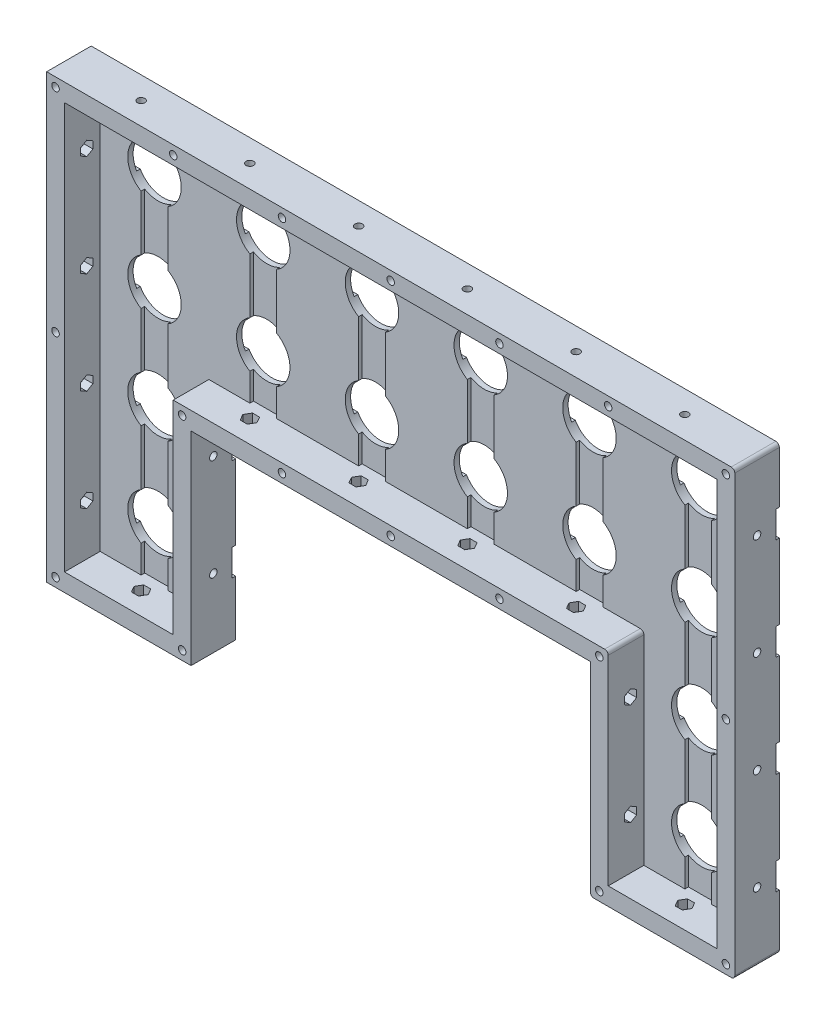
SolidWorks part; units mm, degrees
ref_plane "Alzado" through (0, 0, 0) normal (0, 0, 1) x (1, 0, 0)
ref_plane "Planta" through (0, 0, 0) normal (0, 1, 0) x (1, 0, 0)
ref_plane "Vista lateral" through (0, 0, 0) normal (1, 0, 0) x (0, 0, -1)
sketch "Croquis1" plane through (0, 0, 0) normal (0, 0, 1) x (1, 0, 0)
  line L0 (0, 0) -> (0, 88888.1149) construction
  line L1 (0, 0) -> (88888.1149, 0) construction
  line L2 (-122, -114) -> (-122, 0) construction
  line L3 (-183, 114) -> (183, 114) construction
  line L4 (-183, 114) -> (-183, -114) construction
  line L5 (-183, -114) -> (183, -114) construction
  line L6 (183, 114) -> (183, -114) construction
  line L7 (-183, 114) -> (183, -114) construction
  line L8 (-183, -114) -> (183, 114) construction
  line L9 (-122, 0) -> (0, 0) construction
  line L10 (122, -114) -> (122, 0) construction
  line L11 (-193, -124) -> (193, -124) construction
  line L12 (-193, -124) -> (-193, 124)
  line L13 (-193, 124) -> (193, 124)
  line L14 (193, -124) -> (193, 124)
  line L15 (-193, -124) -> (193, 124) construction
  line L16 (-193, 124) -> (193, -124) construction
  line L17 (-122, 0) -> (122, 0) construction
  line L18 (-122, -114) -> (-183, -114) construction
  line L19 (122, -114) -> (183, -114) construction
  line L20 (-193, -124) -> (-112, -124)
  line L22 (-112, -124) -> (-112, -10)
  line L23 (-112, -10) -> (112, -10)
  line L24 (112, -124) -> (112, -10)
  line L25 (-112, -124) -> (112, -10) construction
  line L26 (-112, -10) -> (112, -124) construction
  line L27 (112, -124) -> (193, -124)
  point P5 (0, 0)
  point P23 (0, -67)
  dimension "D1" = 228
  dimension "D2" = 366
  dimension "D3" = 61
  dimension "D4" = 10
  dimension "D5" = 10
  dimension "D6" = 10
  dimension "D7" = 10
extrude "Saliente-Extruir1" add sketch "Croquis1" along normal blind 25
sketch "Croquis2" plane through (0, 0, 25) normal (0, 0, 1) x (1, 0, 0)
  line L0 (-183, 114) -> (183, 114)
  line L1 (183, 114) -> (183, -114)
  line L2 (183, -114) -> (122, -114)
  line L3 (122, -114) -> (122, 0)
  line L4 (122, 0) -> (-122, 0)
  line L5 (-122, 0) -> (-122, -114)
  line L6 (-122, -114) -> (-183, -114)
  line L7 (-183, -114) -> (-183, 114)
extrude "Cortar-Extruir1" cut sketch "Croquis2" against normal blind 20
sketch "Croquis3" plane through (0, 0, 5) normal (0, 0, 1) x (1, 0, 0)
  line L0 (0, 0) -> (0, 50000) construction
  line L1 (152.5, -114) -> (152.5, 49886) construction
  line L2 (122, -114) -> (183, -114) construction
  line L3 (0, 57) -> (50000, 57) construction
  line L4 (-122, 0) -> (122, 0) construction
  circle A2 centre (30.5, 85.5) radius 15
  circle A3 centre (91.5, 85.5) radius 15
  circle A4 centre (152.5, 85.5) radius 15
  circle A5 centre (91.5, 28.5) radius 15
  circle A6 centre (152.5, 28.5) radius 15
  circle A7 centre (91.5, -28.5) radius 15 [skipped]
  circle A8 centre (152.5, -28.5) radius 15
  circle A9 centre (91.5, -85.5) radius 15 [skipped]
  circle A10 centre (152.5, -85.5) radius 15
  circle A11 centre (30.5, 28.5) radius 15
  circle A12 centre (30.5, -28.5) radius 15 [skipped]
  circle A13 centre (30.5, -85.5) radius 15 [skipped]
  point P7 (152.5, -114)
  dimension "D4" = 30
  dimension "D5" = 3
  dimension "D1" = 61
  dimension "D2" = 57
  dimension "D3" = 57
  dimension "D6" = 4
extrude "Cortar-Extruir2" cut sketch "Croquis3" against normal through all
mirror "Simetría3" about plane through (0, 0, 0) normal (1, 0, 0) of "Cortar-Extruir2"
sketch "Croquis4" plane through (193, 0, 0) normal (1, 0, 0) x (0, 0, -1)
  line L0 (0, -124) -> (0, 124) construction
  line L1 (0, 93) -> (-2, 93)
  line L2 (0, 93) -> (0, 78)
  line L3 (0, 78) -> (-2, 78)
  line L4 (-2, 93) -> (-2, 78)
  line L5 (0, 93) -> (-2, 78) construction
  line L6 (0, 78) -> (-2, 93) construction
  line L7 (0, 0) -> (-50000, 0) construction
  line L8 (0, 36) -> (-2, 36)
  line L9 (0, 36) -> (0, 21)
  line L10 (0, 21) -> (-2, 21)
  line L11 (-2, 36) -> (-2, 21)
  line L12 (0, 36) -> (-2, 21) construction
  line L13 (0, 21) -> (-2, 36) construction
  line L14 (0, -21) -> (-2, -36) construction
  line L19 (0, -36) -> (-2, -21) construction
  line L20 (0, -78) -> (-2, -93) construction
  line L21 (0, -93) -> (-2, -78) construction
  line L22 (-2, -36) -> (-2, -21)
  line L23 (0, -21) -> (-2, -21)
  line L32 (0, -36) -> (0, -21)
  line L33 (0, -36) -> (-2, -36)
  line L34 (-2, -93) -> (-2, -78)
  line L35 (0, -78) -> (-2, -78)
  line L36 (0, -93) -> (0, -78)
  line L37 (0, -93) -> (-2, -93)
  point P4 (-1, 85.5)
  point P11 (-1, 28.5)
  point P24 (-1, -28.5)
  point P25 (-1, -85.5)
  dimension "D1" = 57
  dimension "D2" = 57
  dimension "D3" = 15
  dimension "D4" = 2
extrude "Cortar-Extruir3" cut sketch "Croquis4" against normal through all
sketch "Croquis5" plane through (0, 0, 5) normal (0, 0, 1) x (1, 0, 0)
  line L0 (-152.5, 85.5) -> (-152.5, -49914.5) construction
  line L1 (-91.5, 85.5) -> (-91.5, -49914.5) construction
  line L2 (-30.5, 85.5) -> (-30.5, -49914.5) construction
  line L3 (183, 114) -> (-183, 114) construction
  line L4 (-160, -114) -> (-145, -114)
  line L5 (-160, -114) -> (-160, 114)
  line L6 (-160, 114) -> (-145, 114)
  line L7 (-145, -114) -> (-145, 114)
  line L8 (-160, -114) -> (-145, 114) construction
  line L9 (-160, 114) -> (-145, -114) construction
  line L10 (183, 114) -> (-183, 114) construction
  line L11 (-99, 0) -> (-84, 0)
  line L12 (-99, 0) -> (-99, 114)
  line L13 (-99, 114) -> (-84, 114)
  line L14 (-84, 0) -> (-84, 114)
  line L15 (-99, 0) -> (-84, 114) construction
  line L16 (-99, 114) -> (-84, 0) construction
  line L17 (-122, 0) -> (122, 0) construction
  line L18 (-38, 0) -> (-23, 0)
  line L19 (-38, 0) -> (-38, 114)
  line L20 (-38, 114) -> (-23, 114)
  line L21 (-23, 0) -> (-23, 114)
  line L22 (-38, 0) -> (-23, 114) construction
  line L23 (-38, 114) -> (-23, 0) construction
  line L24 (-183, -114) -> (-122, -114) construction
  point P10 (-152.5, 0)
  point P17 (-91.5, 57)
  point P24 (-30.5, 57)
  dimension "D1" = 15
extrude "Cortar-Extruir4" cut sketch "Croquis5" against normal blind 2
mirror "Simetría4" about plane through (0, 0, 0) normal (1, 0, 0) of "Cortar-Extruir4"
sketch "Croquis6" plane through (0, 124, 0) normal (0, 1, 0) x (1, 0, 0)
  line L0 (0, 0) -> (0, 50000) construction
  line L1 (-203, -12.5) -> (49797, -12.5) construction
  line L2 (-193, -25) -> (-193, 0) construction
  circle A0 centre (30.5, -12.5) radius 2.1
  circle A1 centre (91.5, -12.5) radius 2.1
  circle A2 centre (152.5, -12.5) radius 2.1
  point P9 (-193, -12.5)
  dimension "D1" = 4.2
  dimension "D2" = 61
  dimension "D3" = 61
  dimension "D4" = 61
extrude "Cortar-Extruir5" cut sketch "Croquis6" against normal through all
sketch "Croquis7" plane through (0, 114, 0) normal (0, -1, 0) x (1, 0, 0)
  line L1 (34.4837, 12.5) -> (32.4919, 15.95)
  line L2 (32.4919, 15.95) -> (28.5081, 15.95)
  line L3 (28.5081, 15.95) -> (26.5163, 12.5)
  line L4 (26.5163, 12.5) -> (28.5081, 9.05)
  line L5 (28.5081, 9.05) -> (32.4919, 9.05)
  line L6 (32.4919, 9.05) -> (34.4837, 12.5)
  line L7 (95.4837, 12.5) -> (93.4919, 15.95)
  line L8 (93.4919, 15.95) -> (89.5081, 15.95)
  line L9 (89.5081, 15.95) -> (87.5163, 12.5)
  line L10 (87.5163, 12.5) -> (89.5081, 9.05)
  line L11 (89.5081, 9.05) -> (93.4919, 9.05)
  line L12 (93.4919, 9.05) -> (95.4837, 12.5)
  line L13 (156.4837, 12.5) -> (154.4919, 15.95)
  line L14 (154.4919, 15.95) -> (150.5081, 15.95)
  line L15 (150.5081, 15.95) -> (148.5163, 12.5)
  line L16 (148.5163, 12.5) -> (150.5081, 9.05)
  line L17 (150.5081, 9.05) -> (154.4919, 9.05)
  line L18 (154.4919, 9.05) -> (156.4837, 12.5)
  circle A0 centre (30.5, 12.5) radius 3.45 construction
  circle A1 centre (91.5, 12.5) radius 3.45 construction
  circle A2 centre (152.5, 12.5) radius 3.45 construction
  dimension "D1" = 6.9
extrude "Cortar-Extruir6" cut sketch "Croquis7" against normal offset from surface (5 mm away) 5 up to face at (30.5, 124, 14.6)
sketch "Croquis9" plane through (0, 0, 0) normal (0, 1, 0) x (1, 0, 0)
  line L1 (34.4837, -12.5) -> (32.4919, -9.05)
  line L2 (32.4919, -9.05) -> (28.5081, -9.05)
  line L3 (28.5081, -9.05) -> (26.5163, -12.5)
  line L4 (26.5163, -12.5) -> (28.5081, -15.95)
  line L5 (28.5081, -15.95) -> (32.4919, -15.95)
  line L6 (32.4919, -15.95) -> (34.4837, -12.5)
  line L7 (95.4837, -12.5) -> (93.4919, -9.05)
  line L8 (93.4919, -9.05) -> (89.5081, -9.05)
  line L9 (89.5081, -9.05) -> (87.5163, -12.5)
  line L10 (87.5163, -12.5) -> (89.5081, -15.95)
  line L11 (89.5081, -15.95) -> (93.4919, -15.95)
  line L12 (93.4919, -15.95) -> (95.4837, -12.5)
  circle A0 centre (30.5, -12.5) radius 3.45 construction
  circle A1 centre (91.5, -12.5) radius 3.45 construction
  dimension "D1" = 6.9
extrude "Cortar-Extruir7" cut sketch "Croquis9" against normal offset from surface (5 mm away) 5 up to face at (30.5, -10, 14.6)
sketch "Croquis10" plane through (0, -114, 0) normal (0, 1, 0) x (1, 0, 0)
  line L1 (156.4837, -12.5) -> (154.4919, -9.05)
  line L2 (154.4919, -9.05) -> (150.5081, -9.05)
  line L3 (150.5081, -9.05) -> (148.5163, -12.5)
  line L4 (148.5163, -12.5) -> (150.5081, -15.95)
  line L5 (150.5081, -15.95) -> (154.4919, -15.95)
  line L6 (154.4919, -15.95) -> (156.4837, -12.5)
  circle A0 centre (152.5, -12.5) radius 3.45 construction
  dimension "D1" = 6.9
extrude "Cortar-Extruir8" cut sketch "Croquis10" against normal offset from surface (5 mm away) 5 up to face at (152.5, -124, 14.6)
mirror "Simetría5" about plane through (0, 0, 0) normal (1, 0, 0) of "Cortar-Extruir6", "Cortar-Extruir7", "Cortar-Extruir8", "Cortar-Extruir5"
sketch "Croquis11" plane through (-193, 0, 0) normal (-1, 0, 0) x (0, 0, 1)
  line L0 (12.5, 134) -> (12.5, -49866) construction
  line L1 (25, 124) -> (0, 124) construction
  line L2 (2, 85.5) -> (50002, 85.5) construction
  line L3 (2, 93) -> (2, 78) construction
  circle A0 centre (12.5, 85.5) radius 2.1
  circle A1 centre (12.5, 28.5) radius 2.1
  circle A2 centre (12.5, -28.5) radius 2.1
  circle A3 centre (12.5, -85.5) radius 2.1
  point P4 (12.5, 124)
  point P9 (2, 85.5)
  dimension "D1" = 4.2
  dimension "D2" = 4
extrude "Cortar-Extruir9" cut sketch "Croquis11" against normal through all
sketch "Croquis12" plane through (-183, 0, 0) normal (1, 0, 0) x (0, 0, -1)
  line L1 (-12.5, 81.5163) -> (-9.05, 83.5081)
  line L2 (-9.05, 83.5081) -> (-9.05, 87.4919)
  line L3 (-9.05, 87.4919) -> (-12.5, 89.4837)
  line L4 (-12.5, 89.4837) -> (-15.95, 87.4919)
  line L5 (-15.95, 87.4919) -> (-15.95, 83.5081)
  line L6 (-15.95, 83.5081) -> (-12.5, 81.5163)
  line L7 (-12.5, 24.5163) -> (-9.05, 26.5081)
  line L8 (-9.05, 26.5081) -> (-9.05, 30.4919)
  line L9 (-9.05, 30.4919) -> (-12.5, 32.4837)
  line L10 (-12.5, 32.4837) -> (-15.95, 30.4919)
  line L11 (-15.95, 30.4919) -> (-15.95, 26.5081)
  line L12 (-15.95, 26.5081) -> (-12.5, 24.5163)
  line L13 (-12.5, -32.4837) -> (-9.05, -30.4919)
  line L14 (-9.05, -30.4919) -> (-9.05, -26.5081)
  line L15 (-9.05, -26.5081) -> (-12.5, -24.5163)
  line L16 (-12.5, -24.5163) -> (-15.95, -26.5081)
  line L17 (-15.95, -26.5081) -> (-15.95, -30.4919)
  line L18 (-15.95, -30.4919) -> (-12.5, -32.4837)
  line L19 (-12.5, -89.4837) -> (-9.05, -87.4919)
  line L20 (-9.05, -87.4919) -> (-9.05, -83.5081)
  line L21 (-9.05, -83.5081) -> (-12.5, -81.5163)
  line L22 (-12.5, -81.5163) -> (-15.95, -83.5081)
  line L23 (-15.95, -83.5081) -> (-15.95, -87.4919)
  line L24 (-15.95, -87.4919) -> (-12.5, -89.4837)
  circle A0 centre (-12.5, 85.5) radius 3.45 construction
  circle A1 centre (-12.5, 28.5) radius 3.45 construction
  circle A2 centre (-12.5, -28.5) radius 3.45 construction
  circle A3 centre (-12.5, -85.5) radius 3.45 construction
  dimension "D1" = 6.9
extrude "Cortar-Extruir10" cut sketch "Croquis12" against normal offset from surface (5 mm away) 5 up to face at (-193, 85.5, 14.6)
sketch "Croquis13" plane through (183, 0, 0) normal (-1, 0, 0) x (0, 0, 1)
  line L0 (12.5, 24.5163) -> (15.95, 26.5081)
  line L1 (12.5, 81.5163) -> (15.95, 83.5081)
  line L2 (15.95, 83.5081) -> (15.95, 87.4919)
  line L3 (15.95, 87.4919) -> (12.5, 89.4837)
  line L4 (12.5, 89.4837) -> (9.05, 87.4919)
  line L5 (9.05, 87.4919) -> (9.05, 83.5081)
  line L6 (9.05, 83.5081) -> (12.5, 81.5163)
  line L7 (15.95, 26.5081) -> (15.95, 30.4919)
  line L8 (15.95, 30.4919) -> (12.5, 32.4837)
  line L9 (12.5, 32.4837) -> (9.05, 30.4919)
  line L10 (9.05, 30.4919) -> (9.05, 26.5081)
  line L11 (9.05, 26.5081) -> (12.5, 24.5163)
  line L12 (12.5, -32.4837) -> (15.95, -30.4919)
  line L13 (15.95, -30.4919) -> (15.95, -26.5081)
  line L14 (15.95, -26.5081) -> (12.5, -24.5163)
  line L15 (12.5, -24.5163) -> (9.05, -26.5081)
  line L16 (9.05, -26.5081) -> (9.05, -30.4919)
  line L17 (9.05, -30.4919) -> (12.5, -32.4837)
  line L18 (12.5, -89.4837) -> (15.95, -87.4919)
  line L19 (15.95, -87.4919) -> (15.95, -83.5081)
  line L20 (15.95, -83.5081) -> (12.5, -81.5163)
  line L21 (12.5, -81.5163) -> (9.05, -83.5081)
  line L22 (9.05, -83.5081) -> (9.05, -87.4919)
  line L23 (9.05, -87.4919) -> (12.5, -89.4837)
  circle A0 centre (12.5, 85.5) radius 3.45 construction
  circle A1 centre (12.5, 28.5) radius 3.45 construction
  circle A2 centre (12.5, -28.5) radius 3.45 construction
  circle A3 centre (12.5, -85.5) radius 3.45 construction
  dimension "D1" = 6.9
  dimension "D2" = 4
extrude "Cortar-Extruir11" cut sketch "Croquis13" against normal offset from surface (5 mm away) 5 up to face at (193, 85.5, 14.6)
sketch "Croquis14" plane through (122, 0, 0) normal (1, 0, 0) x (0, 0, -1)
  line L1 (-12.5, -81.5163) -> (-15.95, -83.5081)
  line L2 (-15.95, -83.5081) -> (-15.95, -87.4919)
  line L3 (-15.95, -87.4919) -> (-12.5, -89.4837)
  line L4 (-12.5, -89.4837) -> (-9.05, -87.4919)
  line L5 (-9.05, -87.4919) -> (-9.05, -83.5081)
  line L6 (-9.05, -83.5081) -> (-12.5, -81.5163)
  line L7 (-12.5, -24.5163) -> (-15.95, -26.5081)
  line L8 (-15.95, -26.5081) -> (-15.95, -30.4919)
  line L9 (-15.95, -30.4919) -> (-12.5, -32.4837)
  line L10 (-12.5, -32.4837) -> (-9.05, -30.4919)
  line L11 (-9.05, -30.4919) -> (-9.05, -26.5081)
  line L12 (-9.05, -26.5081) -> (-12.5, -24.5163)
  circle A0 centre (-12.5, -85.5) radius 3.45 construction
  circle A1 centre (-12.5, -28.5) radius 3.45 construction
  dimension "D1" = 6.9
extrude "Cortar-Extruir12" cut sketch "Croquis14" against normal offset from surface (5 mm away) 5 up to face at (112, -28.5, 10.4)
sketch "Croquis15" plane through (-122, 0, 0) normal (-1, 0, 0) x (0, 0, 1)
  line L1 (12.5, -81.5163) -> (9.05, -83.5081)
  line L2 (9.05, -83.5081) -> (9.05, -87.4919)
  line L3 (9.05, -87.4919) -> (12.5, -89.4837)
  line L4 (12.5, -89.4837) -> (15.95, -87.4919)
  line L5 (15.95, -87.4919) -> (15.95, -83.5081)
  line L6 (15.95, -83.5081) -> (12.5, -81.5163)
  line L7 (12.5, -24.5163) -> (9.05, -26.5081)
  line L8 (9.05, -26.5081) -> (9.05, -30.4919)
  line L9 (9.05, -30.4919) -> (12.5, -32.4837)
  line L10 (12.5, -32.4837) -> (15.95, -30.4919)
  line L11 (15.95, -30.4919) -> (15.95, -26.5081)
  line L12 (15.95, -26.5081) -> (12.5, -24.5163)
  circle A0 centre (12.5, -85.5) radius 3.45 construction
  circle A1 centre (12.5, -28.5) radius 3.45 construction
  dimension "D1" = 6.9
extrude "Cortar-Extruir13" cut sketch "Croquis15" against normal offset from surface (5 mm away) 5 up to face at (-112, -28.5, 14.6)
sketch "Croquis16" plane through (0, 0, 25) normal (0, 0, 1) x (1, 0, 0)
  line L0 (-193, 119) -> (49807, 119) construction
  line L1 (0, 0) -> (0, 50000) construction
  line L2 (-188, 124) -> (-188, -49876) construction
  line L3 (-122, 114) -> (-122, 50114) construction
  line L4 (193, 124) -> (-193, 124) construction
  line L5 (-193, 124) -> (-193, -124) construction
  line L6 (-99, 114) -> (-145, 114) construction
  line L7 (-61, 114) -> (-61, 50114) construction
  line L8 (-38, 114) -> (-84, 114) construction
  line L9 (-99, 57) -> (49901, 57) construction
  line L10 (-99, 72.5096) -> (-99, 41.4904) construction
  line L11 (-160, 0) -> (-233.5168, 0) construction
  line L13 (188, 119) -> (188, -49881) construction
  line L14 (-61, -5) -> (49939, -5) construction
  line L15 (117, -124) -> (117, 49876) construction
  line L17 (-117, -124) -> (-117, 49876) construction
  line L19 (-188, -119) -> (49812, -119) construction
  line L20 (112, -10) -> (112, -124) construction
  line L21 (-112, -124) -> (-112, -10) construction
  circle A0 centre (-188, 119) radius 2.1
  circle A1 centre (-122, 119) radius 2.1
  circle A2 centre (-61, 119) radius 2.1
  circle A3 centre (0, 119) radius 2.1
  circle A4 centre (188, 119) radius 2.1
  circle A5 centre (122, 119) radius 2.1
  circle A6 centre (61, 119) radius 2.1
  circle A7 centre (61, -5) radius 2.1
  circle A8 centre (0, -5) radius 2.1
  circle A9 centre (-61, -5) radius 2.1
  circle A10 centre (188, -119) radius 2.1
  circle A11 centre (-188, -119) radius 2.1
  circle A12 centre (-188, 0) radius 2.1
  circle A13 centre (188, 0) radius 2.1
  circle A14 centre (-117, -119) radius 2.1
  circle A15 centre (-117, -5) radius 2.1
  circle A16 centre (117, -5) radius 2.1
  circle A17 centre (117, -119) radius 2.1
  point P17 (-122, 114)
  point P22 (-61, 114)
  point P39 (-99, 57)
  dimension "D3" = 4.2
  dimension "D1" = 5
  dimension "D2" = 5
  dimension "D4" = 5
  dimension "D5" = 5
extrude "Cortar-Extruir14" cut sketch "Croquis16" against normal through all
sketch "Croquis17" plane through (0, 0, 0) normal (0, 0, -1) x (-1, 0, 0)
  line L1 (-184.0163, 119) -> (-186.0081, 122.45)
  line L2 (-186.0081, 122.45) -> (-189.9919, 122.45)
  line L3 (-189.9919, 122.45) -> (-191.9837, 119)
  line L4 (-191.9837, 119) -> (-189.9919, 115.55)
  line L5 (-189.9919, 115.55) -> (-186.0081, 115.55)
  line L6 (-186.0081, 115.55) -> (-184.0163, 119)
  line L7 (-118.0163, 119) -> (-120.0081, 122.45)
  line L8 (-120.0081, 122.45) -> (-123.9919, 122.45)
  line L9 (-123.9919, 122.45) -> (-125.9837, 119)
  line L10 (-125.9837, 119) -> (-123.9919, 115.55)
  line L11 (-123.9919, 115.55) -> (-120.0081, 115.55)
  line L12 (-120.0081, 115.55) -> (-118.0163, 119)
  line L13 (-57.0163, 119) -> (-59.0081, 122.45)
  line L14 (-59.0081, 122.45) -> (-62.9919, 122.45)
  line L15 (-62.9919, 122.45) -> (-64.9837, 119)
  line L16 (-64.9837, 119) -> (-62.9919, 115.55)
  line L17 (-62.9919, 115.55) -> (-59.0081, 115.55)
  line L18 (-59.0081, 115.55) -> (-57.0163, 119)
  line L19 (4.4368, 119) -> (2.2184, 122.8423)
  line L20 (2.2184, 122.8423) -> (-2.2184, 122.8423)
  line L21 (-2.2184, 122.8423) -> (-4.4368, 119)
  line L22 (-4.4368, 119) -> (-2.2184, 115.1577)
  line L23 (-2.2184, 115.1577) -> (2.2184, 115.1577)
  line L24 (2.2184, 115.1577) -> (4.4368, 119)
  line L25 (65.91, 119) -> (63.455, 123.2521)
  line L26 (63.455, 123.2521) -> (58.545, 123.2521)
  line L27 (58.545, 123.2521) -> (56.09, 119)
  line L28 (56.09, 119) -> (58.545, 114.7479)
  line L29 (58.545, 114.7479) -> (63.455, 114.7479)
  line L30 (63.455, 114.7479) -> (65.91, 119)
  line L31 (126.8191, 119) -> (124.4096, 123.1735)
  line L32 (124.4096, 123.1735) -> (119.5904, 123.1735)
  line L33 (119.5904, 123.1735) -> (117.1809, 119)
  line L34 (117.1809, 119) -> (119.5904, 114.8265)
  line L35 (119.5904, 114.8265) -> (124.4096, 114.8265)
  line L36 (124.4096, 114.8265) -> (126.8191, 119)
  line L37 (191.7739, 119) -> (189.8835, 122.2743)
  line L38 (189.8835, 122.2743) -> (186.1026, 122.2743)
  line L39 (186.1026, 122.2743) -> (184.2122, 119)
  line L40 (184.2122, 119) -> (186.1026, 115.7257)
  line L41 (186.1026, 115.7257) -> (189.8835, 115.7257)
  line L42 (189.8835, 115.7257) -> (191.7739, 119)
  line L43 (191.9837, 0) -> (189.9919, 3.45)
  line L44 (189.9919, 3.45) -> (186.0081, 3.45)
  line L45 (186.0081, 3.45) -> (184.0163, 0)
  line L46 (184.0163, 0) -> (186.0081, -3.45)
  line L47 (186.0081, -3.45) -> (189.9919, -3.45)
  line L48 (189.9919, -3.45) -> (191.9837, 0)
  line L49 (191.9837, -119) -> (189.9919, -115.55)
  line L50 (189.9919, -115.55) -> (186.0081, -115.55)
  line L51 (186.0081, -115.55) -> (184.0163, -119)
  line L52 (184.0163, -119) -> (186.0081, -122.45)
  line L53 (186.0081, -122.45) -> (189.9919, -122.45)
  line L54 (189.9919, -122.45) -> (191.9837, -119)
  line L55 (120.9837, -119) -> (118.9919, -115.55)
  line L56 (118.9919, -115.55) -> (115.0081, -115.55)
  line L57 (115.0081, -115.55) -> (113.0163, -119)
  line L58 (113.0163, -119) -> (115.0081, -122.45)
  line L59 (115.0081, -122.45) -> (118.9919, -122.45)
  line L60 (118.9919, -122.45) -> (120.9837, -119)
  line L61 (120.9837, -5) -> (118.9919, -1.55)
  line L62 (118.9919, -1.55) -> (115.0081, -1.55)
  line L63 (115.0081, -1.55) -> (113.0163, -5)
  line L64 (113.0163, -5) -> (115.0081, -8.45)
  line L65 (115.0081, -8.45) -> (118.9919, -8.45)
  line L66 (118.9919, -8.45) -> (120.9837, -5)
  line L67 (64.9837, -5) -> (62.9919, -1.55)
  line L68 (62.9919, -1.55) -> (59.0081, -1.55)
  line L69 (59.0081, -1.55) -> (57.0163, -5)
  line L70 (57.0163, -5) -> (59.0081, -8.45)
  line L71 (59.0081, -8.45) -> (62.9919, -8.45)
  line L72 (62.9919, -8.45) -> (64.9837, -5)
  line L73 (-57.0163, -5) -> (-59.0081, -1.55)
  line L74 (-59.0081, -1.55) -> (-62.9919, -1.55)
  line L75 (-62.9919, -1.55) -> (-64.9837, -5)
  line L76 (-64.9837, -5) -> (-62.9919, -8.45)
  line L77 (-62.9919, -8.45) -> (-59.0081, -8.45)
  line L78 (-59.0081, -8.45) -> (-57.0163, -5)
  line L79 (3.9837, -5) -> (1.9919, -1.55)
  line L80 (1.9919, -1.55) -> (-1.9919, -1.55)
  line L81 (-1.9919, -1.55) -> (-3.9837, -5)
  line L82 (-3.9837, -5) -> (-1.9919, -8.45)
  line L83 (-1.9919, -8.45) -> (1.9919, -8.45)
  line L84 (1.9919, -8.45) -> (3.9837, -5)
  line L85 (-113.0163, -5) -> (-115.0081, -1.55)
  line L86 (-115.0081, -1.55) -> (-118.9919, -1.55)
  line L87 (-118.9919, -1.55) -> (-120.9837, -5)
  line L88 (-120.9837, -5) -> (-118.9919, -8.45)
  line L89 (-118.9919, -8.45) -> (-115.0081, -8.45)
  line L90 (-115.0081, -8.45) -> (-113.0163, -5)
  line L91 (-184.0163, 0) -> (-186.0081, 3.45)
  line L92 (-186.0081, 3.45) -> (-189.9919, 3.45)
  line L93 (-189.9919, 3.45) -> (-191.9837, 0)
  line L94 (-191.9837, 0) -> (-189.9919, -3.45)
  line L95 (-189.9919, -3.45) -> (-186.0081, -3.45)
  line L96 (-186.0081, -3.45) -> (-184.0163, 0)
  line L97 (-184.0163, -119) -> (-186.0081, -115.55)
  line L98 (-186.0081, -115.55) -> (-189.9919, -115.55)
  line L99 (-189.9919, -115.55) -> (-191.9837, -119)
  line L100 (-191.9837, -119) -> (-189.9919, -122.45)
  line L101 (-189.9919, -122.45) -> (-186.0081, -122.45)
  line L102 (-186.0081, -122.45) -> (-184.0163, -119)
  line L103 (-113.0163, -119) -> (-115.0081, -115.55)
  line L104 (-115.0081, -115.55) -> (-118.9919, -115.55)
  line L105 (-118.9919, -115.55) -> (-120.9837, -119)
  line L106 (-120.9837, -119) -> (-118.9919, -122.45)
  line L107 (-118.9919, -122.45) -> (-115.0081, -122.45)
  line L108 (-115.0081, -122.45) -> (-113.0163, -119)
  circle A0 centre (-188, 119) radius 3.45 construction
  circle A1 centre (-122, 119) radius 3.45 construction
  circle A2 centre (-61, 119) radius 3.45 construction
  circle A3 centre (0, 119) radius 3.8423 construction
  circle A4 centre (61, 119) radius 4.2521 construction
  circle A5 centre (122, 119) radius 4.1735 construction
  circle A6 centre (187.9931, 119) radius 3.2743 construction
  circle A7 centre (188, 0) radius 3.45 construction
  circle A8 centre (188, -119) radius 3.45 construction
  circle A9 centre (117, -119) radius 3.45 construction
  circle A10 centre (117, -5) radius 3.45 construction
  circle A11 centre (61, -5) radius 3.45 construction
  circle A12 centre (-61, -5) radius 3.45 construction
  circle A13 centre (0, -5) radius 3.45 construction
  circle A14 centre (-117, -5) radius 3.45 construction
  circle A15 centre (-188, 0) radius 3.45 construction
  circle A16 centre (-188, -119) radius 3.45 construction
  circle A17 centre (-117, -119) radius 3.45 construction
  dimension "D1" = 6.9
extrude "Cortar-Extruir15" cut sketch "Croquis17" against normal blind 10
sketch "Croquis18" plane through (0, 124, 0) normal (0, 1, 0) x (1, 0, 0)
  line L0 (0, 0) -> (0, -50000) construction
  line L1 (-10, 0) -> (-10, -15)
  line L2 (193, 0) -> (-193, 0) construction
  line L3 (-10, -15) -> (10, -15)
  line L4 (10, -15) -> (10, -25)
  line L5 (193, -25) -> (-193, -25) construction
  point P7 (0, -15)
  dimension "D1" = 20
  dimension "D2" = 15
extrude "Cortar-Extruir16" [suppressed] cut sketch "Croquis18" against normal through all
fillet "Redondeo1" radius 2 4 edges at (122, 0, 15) (112, -124, 12.5) (193, -124, 12.5) (193, 124, 12.5)
sketch "Croquis19" [suppressed] plane through (0, 124, 0) normal (0, 1, 0) x (1, 0, 0)
  line L0 (-10, 0) -> (10, 0)
  line L1 (10, 0) -> (10, -15)
  line L2 (10, -15) -> (9.1861, -15)
  line L3 (-10, -15) -> (10, -15) construction
  line L4 (9.1861, -15) -> (5.6042, -0.5676)
  line L5 (5.6042, -0.5676) -> (-10, -0.5676)
  line L6 (-10, -0.5676) -> (-10, 0)
extrude "Saliente-Extruir2" [suppressed] add sketch "Croquis19" against normal up to surface (10 mm away)
sketch "Croquis22" [suppressed] plane through (0, -10, 0) normal (0, -1, 0) x (1, 0, 0)
  line L0 (10, 15) -> (10, 0)
  line L1 (10, 0) -> (-10, 0)
  line L2 (-10, 0) -> (-10, 0.5676)
  line L3 (-10, 0.5676) -> (5.6042, 0.5676)
  line L4 (5.6042, 0.5676) -> (9.1861, 15)
  line L5 (9.1861, 15) -> (10, 15)
extrude "Saliente-Extruir4" [suppressed] add sketch "Croquis22" against normal up to surface (10 mm away)
